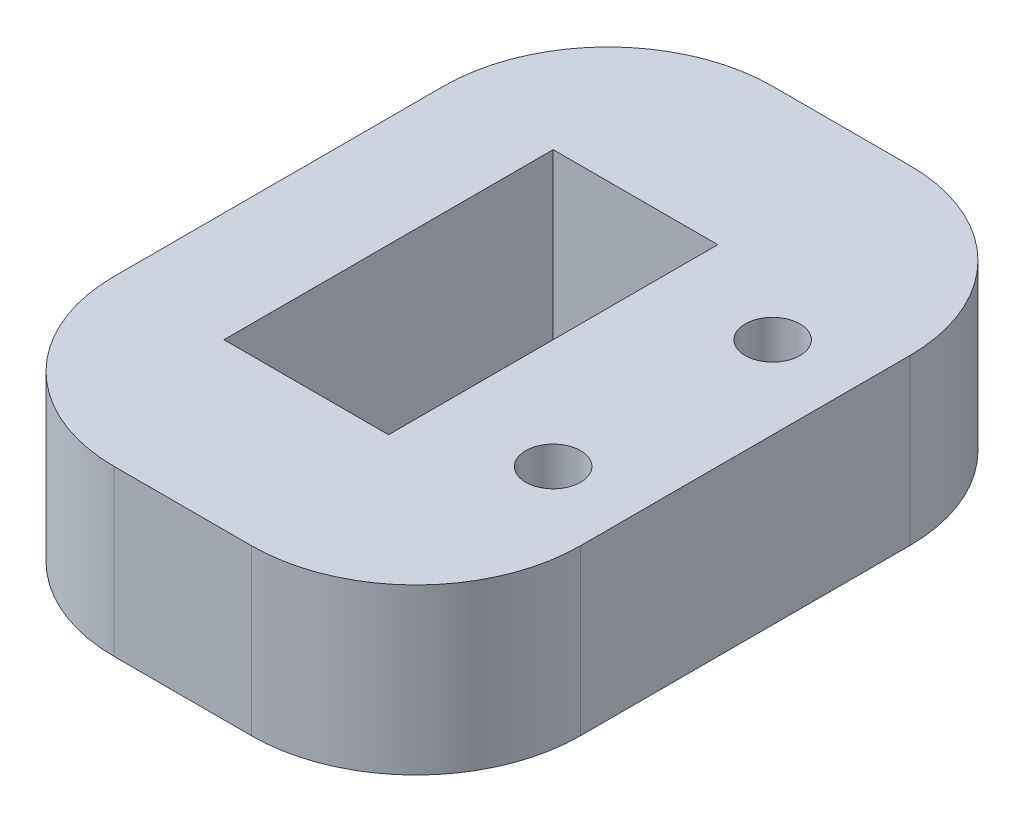
SolidWorks part; units mm, degrees
material "Lasercut ABS"
ref_plane "Front Plane" through (0, 0, 0) normal (0, 0, 1) x (1, 0, 0)
ref_plane "Top Plane" through (0, 0, 0) normal (0, 1, 0) x (1, 0, 0)
ref_plane "Right Plane" through (0, 0, 0) normal (1, 0, 0) x (0, 0, -1)
sketch "Sketch1" plane through (0, 0, 0) normal (0, 1, 0) x (1, 0, 0)
  line L0 (2.75, 2) -> (2.75, -2) construction
  line L1 (-2.25, 3) -> (0.75, 3)
  line L2 (-2.25, 3) -> (-2.25, -3)
  line L3 (-2.25, -3) -> (0.75, -3)
  line L4 (0.75, 3) -> (0.75, -3)
  line L5 (-4.25, 6) -> (4.25, 6)
  line L6 (-4.25, 6) -> (-4.25, -6)
  line L7 (-4.25, -6) -> (4.25, -6)
  line L8 (4.25, 6) -> (4.25, -6)
  circle A0 centre (2.75, 2) radius 0.5
  circle A1 centre (2.75, -2) radius 0.5
  point P12 (2.75, 0)
  point P14 (0.75, 0)
  point P15 (-4.25, 0)
  point P16 (0, 6)
  dimension "D6" = 1
  dimension "D1" = 12
  dimension "D2" = 8.5
  dimension "D3" = 3
  dimension "D4" = 6
  dimension "D5" = 2
  dimension "D7" = 4
  dimension "D8" = 2
extrude "Boss-Extrude1" add sketch "Sketch1" along normal mid plane 3
fillet "Fillet1" radius 3 4 edges at (-4.25, 0, -6) (4.25, 0, -6) (4.25, 0, 6) (-4.25, 0, 6)
